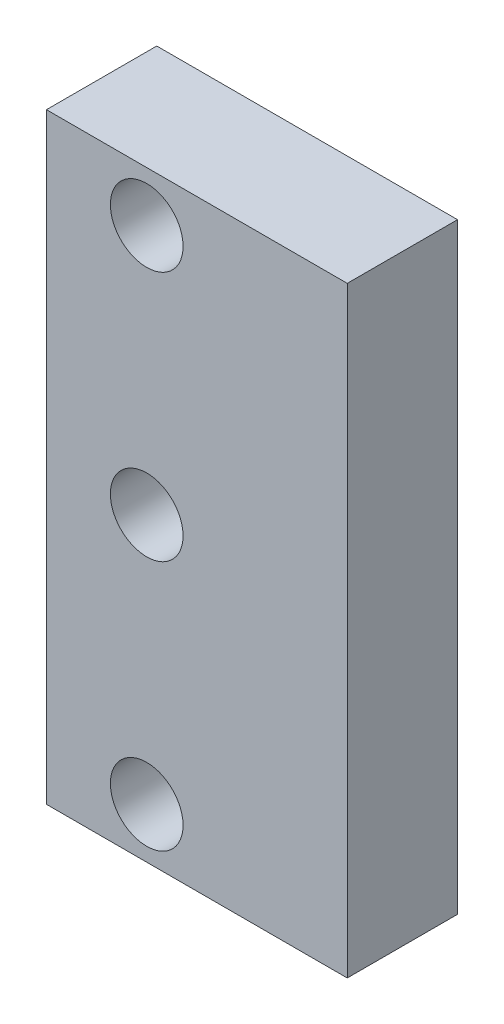
SolidWorks part; units mm, degrees
ref_plane "정면" through (0, 0, 0) normal (0, 0, 1) x (1, 0, 0)
ref_plane "윗면" through (0, 0, 0) normal (0, 1, 0) x (1, 0, 0)
ref_plane "우측면" through (0, 0, 0) normal (1, 0, 0) x (0, 0, -1)
sketch "스케치1" plane through (0, 0, 0) normal (0, 0, 1) x (1, 0, 0)
  line L1 (15, -30) -> (-15, -30)
  line L2 (15, -30) -> (15, 30)
  line L3 (15, 30) -> (-15, 30)
  line L4 (-15, -30) -> (-15, 30)
  line L5 (15, -30) -> (-15, 30) construction
  line L6 (15, 30) -> (-15, -30) construction
  circle A0 centre (-5, 25) radius 3.625
  circle A1 centre (-5, 0) radius 3.625
  circle A2 centre (-5, -25) radius 3.625
  point P0 (0, 0)
  dimension "D3" = 7.25
  dimension "D1" = 30
  dimension "D2" = 10
  dimension "D4" = 25
  dimension "D5" = 25
  dimension "D6" = 60
extrude "보스-돌출1" add sketch "스케치1" along normal blind 11
